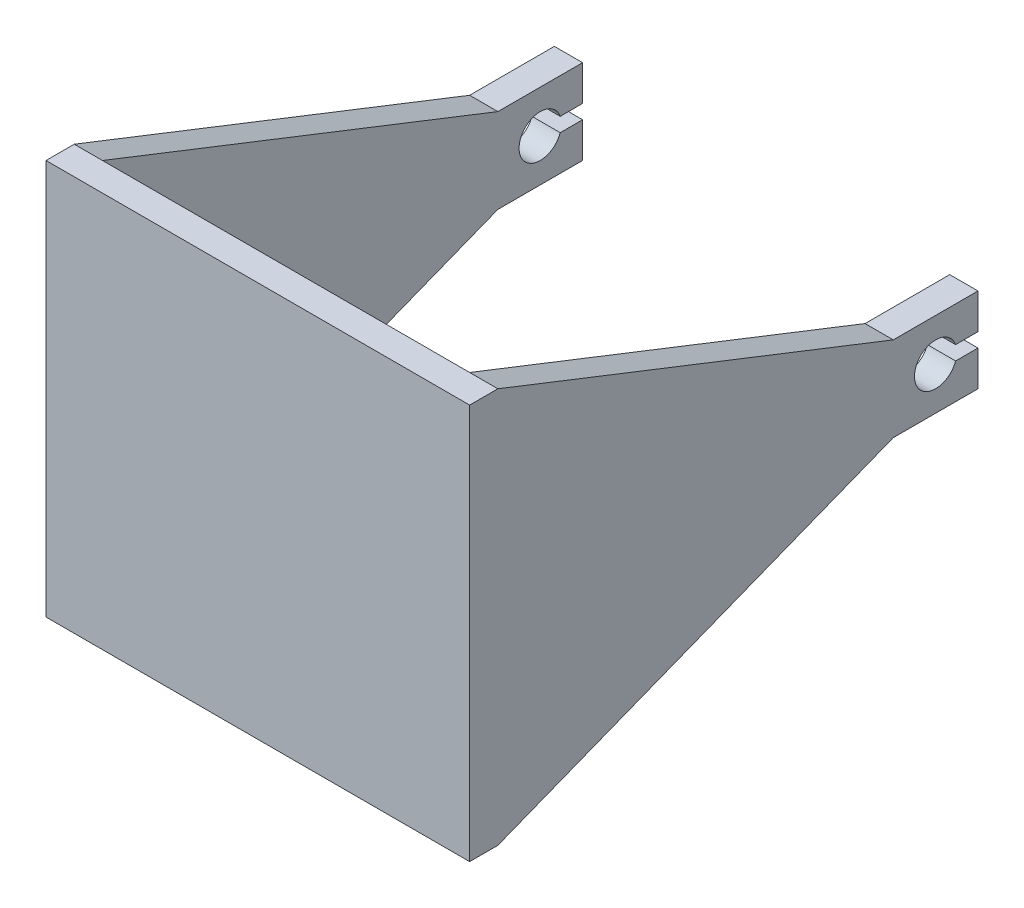
SolidWorks part; units mm, degrees
ref_plane "Front Plane" through (0, 0, 0) normal (0, 0, 1) x (1, 0, 0)
ref_plane "Top Plane" through (0, 0, 0) normal (0, 1, 0) x (1, 0, 0)
ref_plane "Right Plane" through (0, 0, 0) normal (1, 0, 0) x (0, 0, -1)
sketch "Sketch1" plane through (0, 0, 0) normal (0, 0, 1) x (1, 0, 0)
  line L0 (-75, 70) -> (75, -70) construction
  line L1 (75, -70) -> (-75, -70)
  line L2 (75, -70) -> (75, 70)
  line L3 (75, 70) -> (-75, 70)
  line L4 (-75, -70) -> (-75, 70)
  line L5 (-75, -70) -> (75, 70) construction
  line L7 (65, -60) -> (-65, -60)
  line L8 (65, -60) -> (65, 60)
  line L9 (65, 60) -> (-65, 60)
  line L10 (-65, -60) -> (-65, 60)
  point P0 (0, 0)
  point P6 (0, 0)
  point P11 (0, 0)
  dimension "D1" = 140
  dimension "D2" = 150
  dimension "D3" = 10
  dimension "D4" = 10
  dimension "D5" = 10
  dimension "D6" = 10
extrude "Boss-Extrude1" add sketch "Sketch1" along normal blind 150
sketch "Sketch3" plane through (75, 0, 0) normal (1, 0, 0) x (0, 0, -1)
  line L0 (0, 15) -> (30, 15)
  line L1 (0, -70) -> (0, 70) construction
  line L2 (30, 15) -> (30, 2.5)
  line L3 (30, -15) -> (0, -15)
  line L4 (0, -15) -> (0, 15)
  line L5 (15, 15) -> (15, -15) construction
  line L6 (22.5, 0) -> (0, 0) construction
  line L7 (22.0711, 2.5) -> (30, 2.5)
  line L8 (22.5, 0) -> (33.1097, 0) construction
  line L9 (30, -2.5) -> (22.0711, -2.5)
  line L10 (30, -2.5) -> (30, -15)
  line L11 (27.169, 0) -> (27.169, -2.5) construction
  line L12 (25.4494, 0) -> (25.4494, 2.5) construction
  circle A0 centre (15, 0) radius 7.5
  point P6 (0, 0)
  line M10 (0, -70) -> (0, 70)
  dimension "D3" = 15
  dimension "D1" = 30
  dimension "D2" = 30
  dimension "D4" = 2.5
extrude "Boss-Extrude2" add sketch "Sketch3" against normal up to surface (10 mm away) contours A0 L7 L2 L0 L3 L10 L9 M10 up to face at (65, 0, 75)
sketch "Sketch4" plane through (-75, 0, 0) normal (-1, 0, 0) x (0, 0, 1)
  line L0 (-30, -2.5) -> (-22.0711, -2.5) construction
  line L1 (-30, -2.5) -> (-30, -15) construction
  line L2 (-30, -15) -> (0, -15) construction
  line L3 (0, -15) -> (0, 15) construction
  line L4 (0, 70) -> (0, -70)
  line L5 (0, -70) -> (150, -70)
  line L6 (150, -70) -> (150, 70)
  line L7 (150, 70) -> (0, 70)
  line L8 (0, 70) -> (0, -70)
  line L9 (0, -70) -> (150, -70)
  line L10 (150, -70) -> (150, 70)
  line L11 (150, 70) -> (0, 70)
  line L12 (0, 15) -> (-30, 15) construction
  line L13 (-30, 15) -> (-30, 2.5) construction
  line L14 (-22.0711, 2.5) -> (-30, 2.5) construction
  line L15 (-30, -2.5) -> (-22.0711, -2.5)
  line L16 (-30, -2.5) -> (-30, -15)
  line L17 (-30, -15) -> (0, -15)
  line L18 (0, -15) -> (0, 15)
  line L19 (0, 15) -> (-30, 15)
  line L20 (-30, 15) -> (-30, 2.5)
  line L21 (-22.0711, 2.5) -> (-30, 2.5)
  circle A1 centre (-15, 0) radius 7.5
  circle A2 centre (-15, 0) radius 7.5
  dimension "D1" = 0
  dimension "D2" = 0
extrude "Boss-Extrude3" add sketch "Sketch4" along direction (1, 0, 0) on the side against the normal up to surface (10 mm away) contours A2 L15 L16 L17 L8 L19 L20 L21
sketch "Sketch7" plane through (0, -70, 0) normal (0, -1, 0) x (1, 0, 0)
  line L0 (-75, 150) -> (75, 150) construction
  line L1 (65, 0) -> (-65, 0)
  line L2 (65, 0) -> (65, 150)
  line L3 (65, 150) -> (-65, 150)
  line L4 (-65, 0) -> (-65, 150)
  point P7 (0, 0)
extrude "Cut-Extrude2" cut sketch "Sketch7" against normal up to surface (140 mm away) up to face at (0, 70, 75)
sketch "Sketch8" plane through (-75, 0, 0) normal (-1, 0, 0) x (0, 0, 1)
  line L0 (150, 70) -> (0, 70) construction
  line L1 (150, -70) -> (140, -70)
  line L2 (150, -70) -> (150, 70)
  line L3 (150, 70) -> (140, 70)
  line L4 (140, -70) -> (140, 70)
  dimension "D1" = 10
extrude "Boss-Extrude4" add sketch "Sketch8" against normal up to surface (150 mm away) up to face at (75, 0, 12.5357)
sketch "Sketch9" plane through (-75, 0, 0) normal (-1, 0, 0) x (0, 0, 1)
  line L0 (0, -15) -> (140, -70)
  line L1 (140, -70) -> (0, -70)
  line L2 (0, -70) -> (0, -15)
  line L3 (0, 15) -> (0, 70)
  line L4 (0, 70) -> (140, 70)
  line L5 (140, 70) -> (0, 15)
extrude "Cut-Extrude3" cut sketch "Sketch9" against normal up to surface (150 mm away) and the other way through all up to face at (75, 0, 12.5357)
sketch "Sketch11" plane through (0, -70, 0) normal (0, -1, 0) x (1, 0, 0)
  line L0 (-75, 150) -> (75, 150) construction
  point P0 (0, 150)
